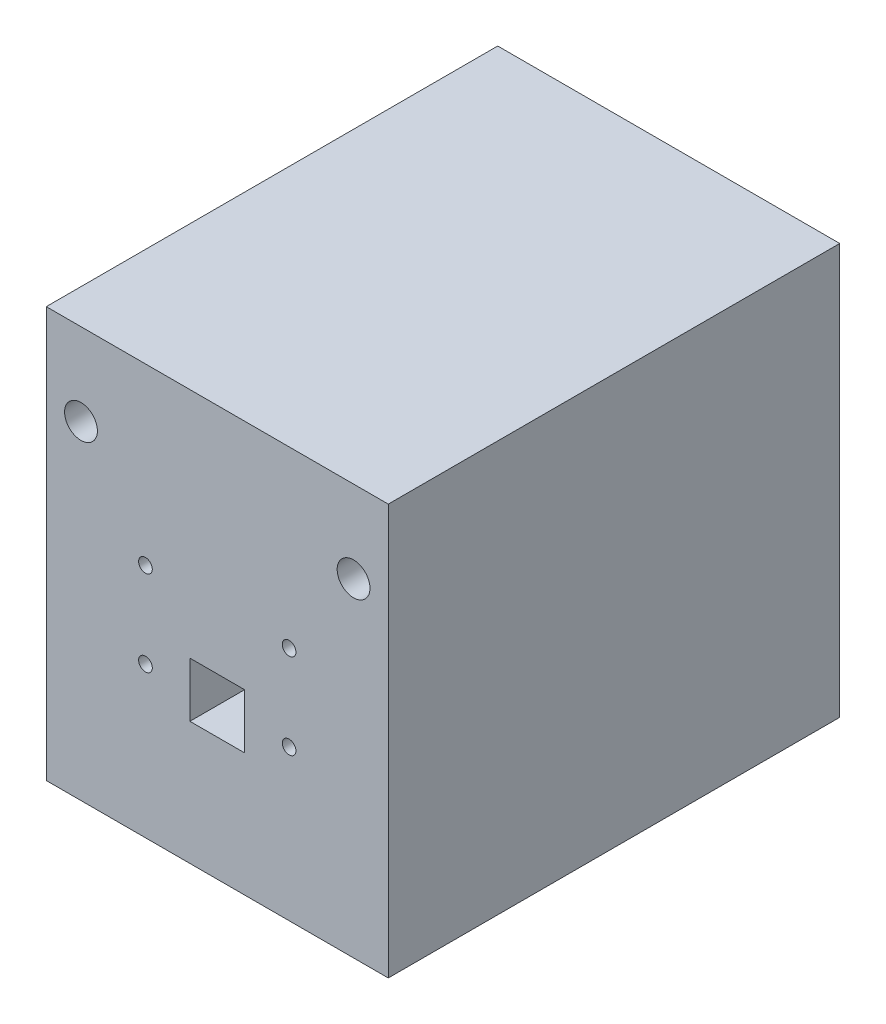
SolidWorks part; units mm, degrees
ref_plane "Front" through (0, 0, 0) normal (0, 0, 1) x (1, 0, 0)
ref_plane "Top" through (0, 0, 0) normal (0, 1, 0) x (1, 0, 0)
ref_plane "Right" through (0, 0, 0) normal (1, 0, 0) x (0, 0, -1)
sketch "Sketch1" plane through (0, 0, 0) normal (0, 0, 1) x (1, 0, 0)
  line L0 (-22.3742, 22) -> (-1.3742, 22) construction
  line L1 (0, 0) -> (-25, 0) construction
  line L5 (-15.8742, 26) -> (-7.8742, 26)
  line L6 (-15.8742, 26) -> (-15.8742, 18)
  line L7 (-15.8742, 18) -> (-7.8742, 18)
  line L8 (-7.8742, 26) -> (-7.8742, 18)
  line L9 (-22.3742, 34.5) -> (-1.3742, 34.5) construction
  line L10 (-22.3742, 12.5) -> (-1, 12.5) construction
  line L11 (-31.7992, 48) -> (8.0508, 48) construction
  line L13 (-36.8742, 60) -> (13.1258, 60)
  line L14 (-36.8742, 60) -> (-36.8742, 0)
  line L15 (-36.8742, 0) -> (13.1258, 0)
  line L16 (13.1258, 60) -> (13.1258, 0)
  circle A0 centre (-22.3742, 34.5) radius 1
  circle A1 centre (-22.3742, 22) radius 1
  circle A2 centre (-1.3742, 22) radius 1
  circle A3 centre (-1.3742, 34.5) radius 1
  circle A4 centre (-31.7992, 48) radius 2.4
  circle A5 centre (8.0508, 48) radius 2.4
  point P1 (-21.3742, 16.7645)
  point P2 (0, 0)
  dimension "D2" = 2
  dimension "D13" = 4.8
  dimension "D1" = 8
  dimension "D3" = 21
  dimension "D4" = 18
  dimension "D5" = 21
  dimension "D7" = 5.5
  dimension "D8" = 12.5
  dimension "D10" = 14.5
  dimension "D11" = 9.5
  dimension "D12" = 39.85
  dimension "D14" = 50
  dimension "D15" = 60
  dimension "D16" = 5.075
  dimension "D18" = 12
extrude "Boss-Extrude1" add sketch "Sketch1" along normal blind 66
